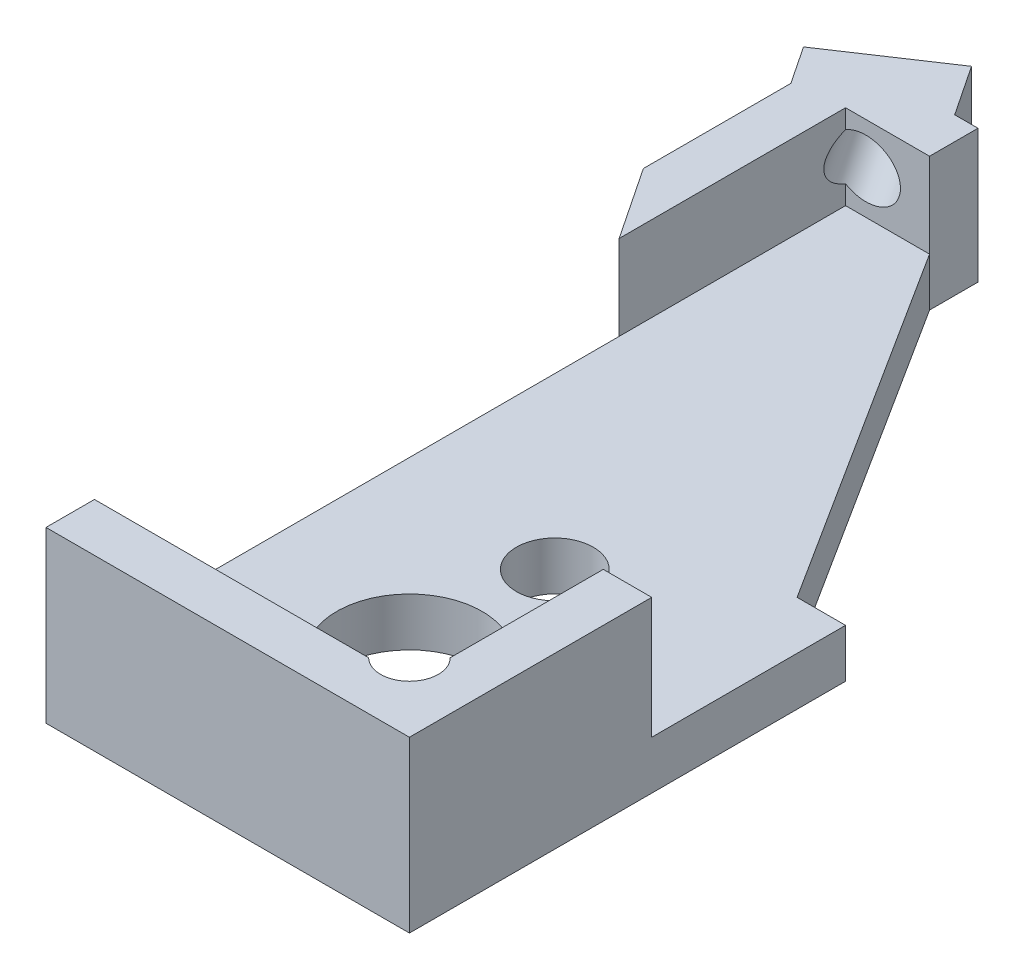
SolidWorks part; units mm, degrees
ref_plane "Front Plane" through (0, 0, 0) normal (0, 0, 1) x (1, 0, 0)
ref_plane "Top Plane" through (0, 0, 0) normal (0, 1, 0) x (1, 0, 0)
ref_plane "Right Plane" through (0, 0, 0) normal (1, 0, 0) x (0, 0, -1)
sketch "Sketch1" plane through (0, 0, 0) normal (0, 1, 0) x (1, 0, 0)
  line L7 (4.25, 8.75) -> (-4.25, 8.75)
  line L8 (4.25, 8.75) -> (4.25, -8.75)
  line L9 (4.25, -8.75) -> (-4.25, -8.75)
  line L10 (-4.25, 8.75) -> (-4.25, -8.75)
  line L11 (4.25, 8.75) -> (-4.25, -8.75) construction
  line L12 (4.25, -8.75) -> (-4.25, 8.75) construction
  point P0 (0, 0)
  point P6 (0, 0)
  dimension "D1" = 8.5
  dimension "D2" = 17.5
extrude "Boss-Extrude1" add sketch "Sketch1" along normal blind 3.5
sketch "Sketch2" plane through (0, 3.5, 0) normal (0, 1, 0) x (1, 0, 0)
  line L0 (-4.25, 8.75) -> (-4.25, -8.75) construction
  line L1 (3.25, 7.75) -> (-3.25, 7.75)
  line L2 (3.25, 7.75) -> (3.25, -7.75)
  line L3 (3.25, -7.75) -> (-3.25, -7.75)
  line L4 (-3.25, 7.75) -> (-3.25, -7.75)
  line L5 (3.25, 7.75) -> (-3.25, -7.75) construction
  line L6 (3.25, -7.75) -> (-3.25, 7.75) construction
  line L7 (4.25, 8.75) -> (-4.25, 8.75) construction
  point P0 (0, 0)
  dimension "D1" = 1
  dimension "D2" = 1
extrude "Cut-Extrude1" cut sketch "Sketch2" against normal offset from surface (2.5 mm away) 1 up to face at (0, 0, 0)
sketch "Sketch3" plane through (0, 1, 0) normal (0, 1, 0) x (1, 0, 0)
  line L0 (-3.25, -7.75) -> (3.25, -7.75) construction
  line L1 (3.25, -7.75) -> (3.25, 7.75) construction
  circle A0 centre (0.25, -4.75) radius 1.5
  dimension "D1" = 3
  dimension "D2" = 3
  dimension "D3" = 3
extrude "Cut-Extrude2" cut sketch "Sketch3" against normal through all
sketch "Sketch6" plane through (0, 3.5, 0) normal (0, 1, 0) x (1, 0, 0)
  line L0 (3.25, -7.75) -> (3.25, 7.75) construction
  line L2 (-3.25, -7.75) -> (3.25, -7.75) construction
  line L3 (3.25, -7.3291) -> (2.8291, -7.3291) construction
  line L4 (2.8291, -7.3291) -> (2.8291, -7.75) construction
  circle A3 centre (2.8291, -7.3291) radius 0.5953
  dimension "D1" = 1.1906
extrude "Cut-Extrude5" cut sketch "Sketch6" against normal up to surface (2.5 mm away) up to face at (0.25, 1, 6.25)
sketch "Sketch7" plane through (0, 1, 0) normal (0, 1, 0) x (1, 0, 0)
  line L0 (2.125, -1.75) -> (-1.625, -1.75) construction
  line L1 (-1.625, -1.75) -> (-1.625, -6.5) construction
  line L2 (-1.625, -6.5) -> (2.125, -6.5) construction
  line L3 (2.125, -6.5) -> (2.125, -1.75) construction
  line L4 (0.25, -1.75) -> (0.25, -4.75) construction
  circle A0 centre (0.25, -1.75) radius 0.7937
  circle A2 centre (-1.625, -6.5) radius 0.7938
  circle A3 centre (2.125, -6.5) radius 0.7938
  circle A4 centre (0.25, -4.75) radius 1.5 construction
  dimension "D1" = 1.5875
  dimension "D2" = 3.75
  dimension "D3" = 3
  dimension "D4" = 1.75
extrude "Cut-Extrude6" cut sketch "Sketch7" against normal through all
sketch "Sketch9" plane through (0, 3.5, 0) normal (0, 1, 0) x (1, 0, 0)
  line L0 (-2.6906, 9.7896) -> (-4.7708, 8.4028)
  line L1 (-3.4116, 7.6422) -> (-4.0015, 7.249)
  line L2 (-3.4116, 7.6422) -> (-2.5113, 8.2425)
  line L3 (-2.6906, 9.7896) -> (-1.9214, 8.6357)
  line L5 (3.25, -7.75) -> (-2.75, -7.75) construction
  line L6 (-3.25, -7.75) -> (2.4081, -7.75) construction
  line L7 (-4.25, -8.75) -> (4.25, -8.75) construction
  line L8 (-2.75, -7.75) -> (-2.75, 7.25) construction
  line L9 (-2.75, 7.25) -> (3.25, 7.25) construction
  line L10 (3.25, -6.9081) -> (3.25, 7.75) construction
  line L11 (3.25, 7.25) -> (3.25, -7.75) construction
  line L12 (-2.75, 6.6498) -> (-1.8497, 7.25) construction
  line L13 (-2.75, 6.6498) -> (-3.4116, 7.6422) construction
  line L14 (-2.2998, 6.9499) -> (-2.9615, 7.9423) construction
  line L15 (-1.9214, 8.6357) -> (-2.5113, 8.2425)
  line L16 (-4.0015, 7.249) -> (-4.7708, 8.4028)
  line L17 (-2.9615, 7.9423) -> (-3.7307, 9.0962) construction
  dimension "D1" = 6
  dimension "D2" = 15
  dimension "D3" = 1.082
  dimension "D4" = 2.5
  dimension "D5" = 33.69
  dimension "D6" = 1
extrude "Boss-Extrude2" add sketch "Sketch9" against normal up to surface (3.5 mm away) up to face at (2.125, 0, 7.2937)
sketch "Sketch14" plane through (0, 3.5, 0) normal (0, 1, 0) x (1, 0, 0)
  line L1 (-6.2555, 2.3016) -> (-0.2445, 2.3016)
  line L2 (-6.2555, 2.3016) -> (-6.2555, 13.1984)
  line L3 (-6.2555, 13.1984) -> (-0.2445, 13.1984)
  line L4 (-0.2445, 2.3016) -> (-0.2445, 13.1984)
  line L5 (-6.2555, 2.3016) -> (-0.2445, 13.1984) construction
  line L6 (-6.2555, 13.1984) -> (-0.2445, 2.3016) construction
  point P0 (-3.25, 7.75)
extrude "Cut-Extrude8" cut sketch "Sketch14" against normal blind 0.75
sketch "Sketch10" plane through (-5.3462, 0, -8.0192) normal (-0.5547, 0, -0.8321) x (-0.8321, 0, 0.5547)
  line L0 (-1.9415, 1) -> (-1.9415, 1.875) construction
  line L1 (-3.1915, 2.75) -> (-0.6915, 2.75) construction
  line L2 (-1.9415, 1.875) -> (-1.9415, 2.75) construction
  line L4 (-1.9415, 1) -> (-1.9415, 0) construction
  line L5 (-3.1915, 0) -> (-0.6915, 0) construction
  dimension "D1" = 1
hole_wizard "Tap Drill for #0-80 Tap1" positions "Sketch12" profile "Sketch11" hole size "#0-80" standard "ANSI Inch"
sketch "Sketch12" plane through (-5.3462, 0, -8.0192) normal (-0.5547, 0, -0.8321) x (-0.8321, 0, 0.5547)
  point P0 (-1.9415, 1.875)
sketch "Sketch11" plane through (-3.7307, 1.875, -9.0962) normal (0, 1, 0) x (-0.8321, 0, 0.5547)
  line L0 (0, 0) -> (0, 7.4679)
  line L1 (0, 7.4679) -> (0.5956, 7.11)
  line L2 (0.5956, 7.11) -> (0.5956, 0)
  line L5 (0.5956, 0) -> (0, 0)
  line L10 (0, 7.4679) -> (-0.5956, 7.11) construction
  line L11 (0, -6.35) -> (0, 107.95) construction
  dimension "Hole Dia." = 1.1913
  dimension "Hole Depth" = 7.11
  dimension "Drill Angle" = 118
sketch "Sketch13" plane through (0, 3.5, 0) normal (0, 1, 0) x (1, 0, 0)
  line L0 (-3.2496, -8.75) -> (-4.25, -8.75)
  line L1 (3.25, 0.25) -> (-1.5171, 7.75)
  line L2 (-4.25, -8.75) -> (4.25, -8.75) construction
  line L3 (3.25, -6.9081) -> (3.25, 7.75) construction
  line L4 (3.25, 7.75) -> (-3.25, 7.75) construction
  line L5 (-1.5171, 7.75) -> (-1.5171, 8.75)
  line L6 (-1.9976, 8.75) -> (-0.2445, 8.75) construction
  line L7 (-1.5171, 8.75) -> (4.25, 8.75)
  line L8 (-3.25, -7.75) -> (2.4081, -7.75) construction
  line L10 (-4.25, -8.75) -> (-4.25, 4.5776)
  line L12 (-4.25, 4.5776) -> (-3.2496, 3.077)
  line L13 (-3.2496, 3.077) -> (-3.2496, -8.75)
  line L14 (4.25, 8.75) -> (4.25, 0.25)
  line L15 (4.25, -8.75) -> (4.25, 8.75) construction
  line L16 (4.25, 0.25) -> (3.25, 0.25)
  line L17 (-4.7708, 8.4028) -> (-4.25, 7.6217) construction
  dimension "D1" = 8
extrude "Cut-Extrude7" cut sketch "Sketch13" against normal up to next
sketch "Sketch15" plane through (0, 3.5, 0) normal (0, 1, 0) x (1, 0, 0)
  line L0 (3.25, -6.9081) -> (3.25, 0.25) construction
  line L1 (4.25, 0.25) -> (3.25, 0.25)
  line L2 (4.25, 0.25) -> (4.25, -3.75)
  line L3 (4.25, -3.75) -> (3.25, -3.75)
  line L4 (3.25, 0.25) -> (3.25, -3.75)
  line L5 (-3.2496, -8.75) -> (4.25, -8.75) construction
  dimension "D1" = 5
extrude "Cut-Extrude9" cut sketch "Sketch15" against normal blind 2.5
